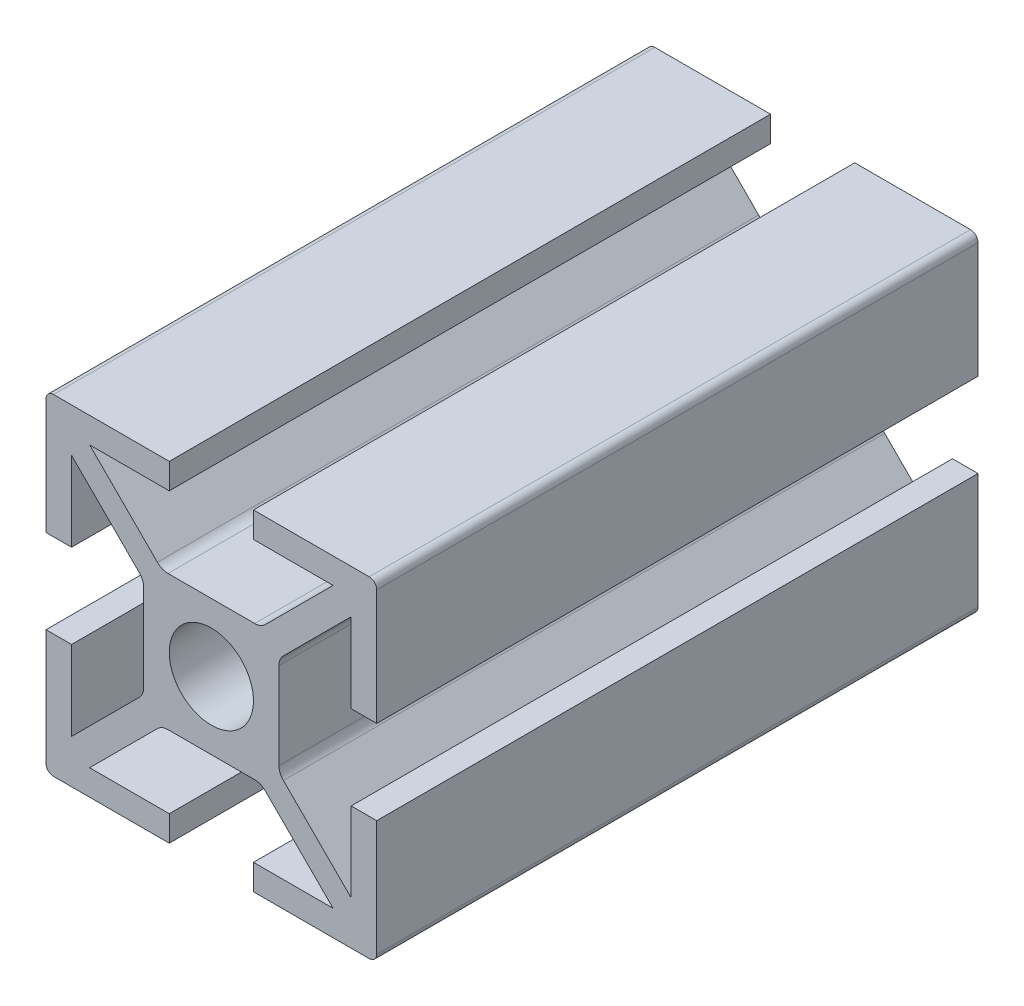
SolidWorks part; units mm, degrees
ref_plane "Plan de face" through (0, 0, 0) normal (0, 0, 1) x (1, 0, 0)
ref_plane "Plan de dessus" through (0, 0, 0) normal (0, 1, 0) x (1, 0, 0)
ref_plane "Plan de droite" through (0, 0, 0) normal (1, 0, 0) x (0, 0, -1)
sketch "Esquisse1" plane through (0, 0, 0) normal (0, 0, 1) x (1, 0, 0)
  line L0 (0, 22) -> (0, -5.6123) construction
  line L1 (-20.8753, 0) -> (5.9514, 0) construction
  line L2 (-2.8, 11) -> (-2.8, 9.3)
  line L3 (-9.3, 2.8) -> (-9.3, 8.0979)
  line L4 (-9.3, 8.0979) -> (-4.5, 3.2979)
  line L5 (-11, 2.8) -> (-11, 11)
  line L6 (-11, 11) -> (-2.8, 11)
  line L7 (-9.3, 2.8) -> (-11, 2.8)
  line L8 (-8.0979, 9.3) -> (-2.8, 9.3)
  line L9 (-8.0979, 9.3) -> (-3.2979, 4.5)
  line L10 (-3.2979, 4.5) -> (3.2979, 4.5)
  line L11 (-4.5, 3.2979) -> (-4.5, -3.2979)
  line L12 (8.0979, 9.3) -> (3.2979, 4.5)
  line L13 (8.0979, 9.3) -> (2.8, 9.3)
  line L14 (2.8, 11) -> (2.8, 9.3)
  line L15 (11, 11) -> (2.8, 11)
  line L16 (11, 2.8) -> (11, 11)
  line L17 (9.3, 2.8) -> (11, 2.8)
  line L18 (9.3, 2.8) -> (9.3, 8.0979)
  line L19 (4.5, 3.2979) -> (4.5, -3.2979)
  line L20 (9.3, 8.0979) -> (4.5, 3.2979)
  line L21 (9.3, -2.8) -> (11, -2.8)
  line L22 (9.3, -8.0979) -> (4.5, -3.2979)
  line L23 (9.3, -2.8) -> (9.3, -8.0979)
  line L24 (11, -2.8) -> (11, -11)
  line L25 (11, -11) -> (2.8, -11)
  line L26 (8.0979, -9.3) -> (3.2979, -4.5)
  line L27 (2.8, -11) -> (2.8, -9.3)
  line L28 (8.0979, -9.3) -> (2.8, -9.3)
  line L29 (-11, -11) -> (-2.8, -11)
  line L30 (-2.8, -11) -> (-2.8, -9.3)
  line L31 (-8.0979, -9.3) -> (-2.8, -9.3)
  line L32 (-3.2979, -4.5) -> (3.2979, -4.5)
  line L33 (-8.0979, -9.3) -> (-3.2979, -4.5)
  line L34 (-9.3, -8.0979) -> (-4.5, -3.2979)
  line L35 (-9.3, -2.8) -> (-9.3, -8.0979)
  line L36 (-9.3, -2.8) -> (-11, -2.8)
  line L37 (-11, -2.8) -> (-11, -11)
  point P17 (0, 4.5)
  point P27 (4.5, 0)
  point P41 (-4.5, 0)
  dimension "D1" = 11
  dimension "D2" = 11
  dimension "D3" = 2.8
  dimension "D4" = 2.8
  dimension "D5" = 1.7
  dimension "D6" = 1.7
  dimension "D7" = 1.7
  dimension "D8" = 1.7
  dimension "D9" = 4.8
  dimension "D10" = 4.8
extrude "Extrusion1" add sketch "Esquisse1" along normal blind 40
sketch "Esquisse2" plane through (0, 0, 0) normal (0, 0, -1) x (-1, 0, 0)
  circle A0 centre (0, 0) radius 2.8
  dimension "D1" = 5.6
extrude "Enlèv. mat.-Extru.1" cut sketch "Esquisse2" against normal through all
fillet "Congé1" radius 0.5 4 edges at (11, -11, 20) (-11, -11, 20) (-11, 11, 20) (11, 11, 20)
fillet "Congé2" radius 1 8 edges at (-4.5, -3.2979, 20) (-4.5, 3.2979, 20) (3.2979, -4.5, 20) (-3.2979, -4.5, 20) (4.5, -3.2979, 20) (4.5, 3.2979, 20) (-3.2979, 4.5, 20) (3.2979, 4.5, 20)
